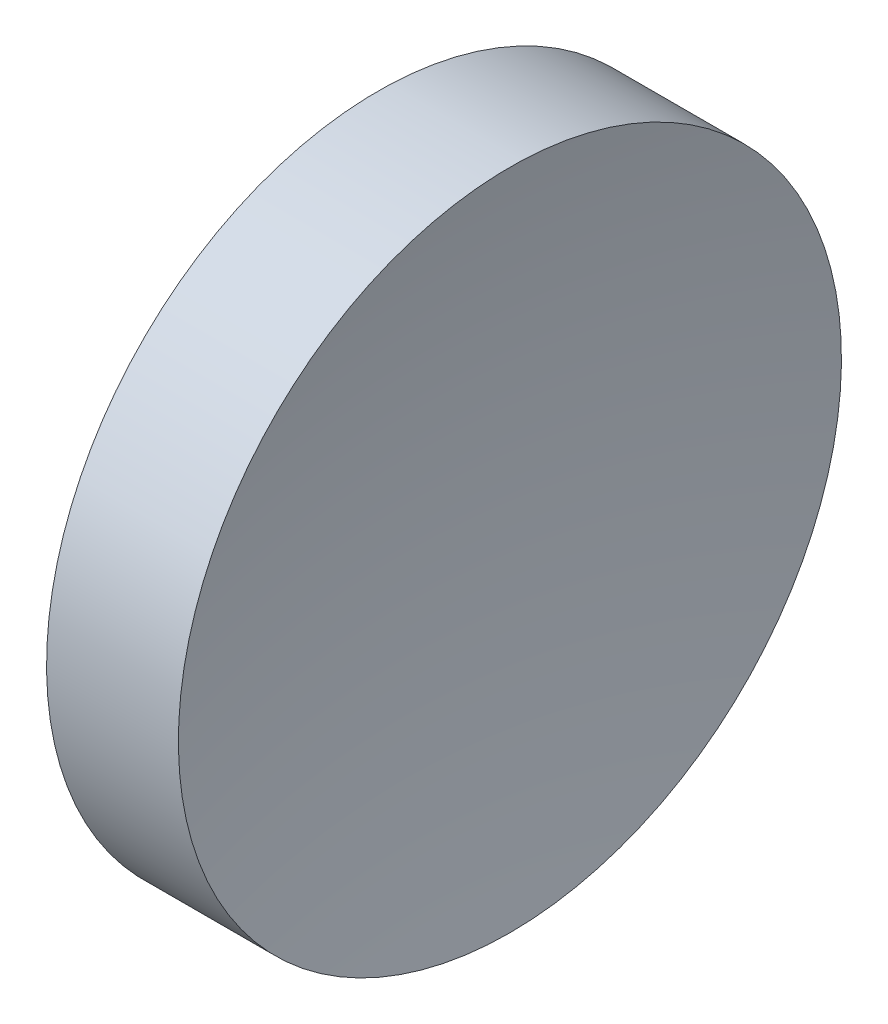
SolidWorks part; units mm, degrees
ref_plane "前视基准面" through (0, 0, 0) normal (0, 0, 1) x (1, 0, 0)
ref_plane "上视基准面" through (0, 0, 0) normal (0, 1, 0) x (1, 0, 0)
ref_plane "右视基准面" through (0, 0, 0) normal (1, 0, 0) x (0, 0, -1)
sketch "草图1" plane through (0, 0, 0) normal (0, 0, 1) x (1, 0, 0)
  line L0 (21.506, 13.0311) -> (26.997, 13.0311) construction
  line L1 (22.4242, 13.0311) -> (22.4242, 18.0311)
  line L2 (22.4242, 18.0311) -> (24.4126, 18.0311)
  line L3 (23.9242, 13.0311) -> (22.4242, 13.0311)
  arc A0 (24.4126, 18.0311) -> (23.9242, 13.0311) centre (49.7642, 13.0311) ccw
revolve "旋转1" add sketch "草图1" angle 360 about L0
